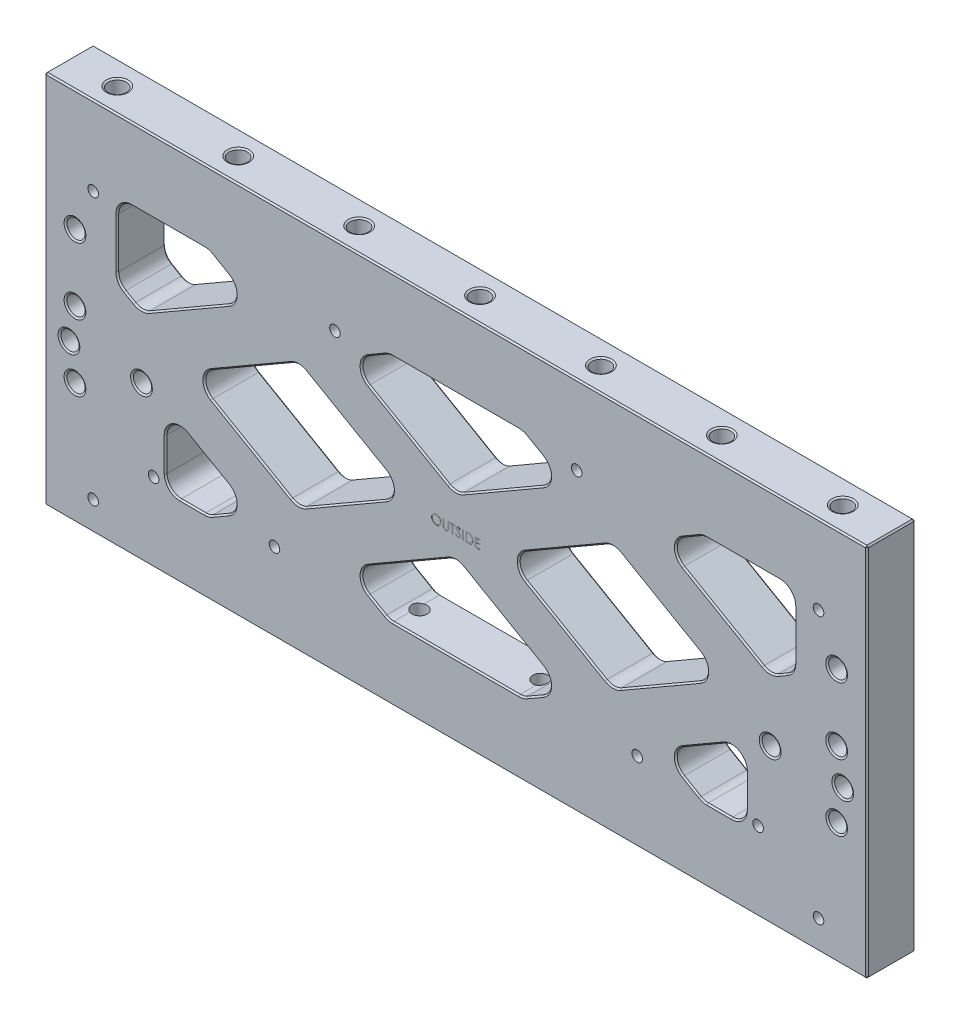
SolidWorks part; units mm, degrees
material "6061-T6 Al"
ref_plane "Front" through (0, 0, 0) normal (0, 0, 1) x (1, 0, 0)
ref_plane "Top" through (0, 0, 0) normal (0, 1, 0) x (1, 0, 0)
ref_plane "Right" through (0, 0, 0) normal (1, 0, 0) x (0, 0, -1)
sketch "Sketch1" plane through (0, 0, 0) normal (0, 0, 1) x (1, 0, 0)
  line L1 (-215.9, 196.85) -> (215.9, 196.85)
  line L2 (-215.9, 196.85) -> (-215.9, 0)
  line L3 (-215.9, 0) -> (215.9, 0)
  line L4 (215.9, 196.85) -> (215.9, 0)
  dimension "D1" = 431.8
  dimension "D2" = 196.85
extrude "Extrude1" add sketch "Sketch1" along normal blind 25.4
sketch "Sketch8" plane through (0, 0, 25.4) normal (0, 0, 1) x (1, 0, 0)
  line L0 (0, 158.75) -> (0, 196.85) construction
  line L1 (-177.8, 158.75) -> (177.8, 158.75)
  line L2 (-177.8, 158.75) -> (-177.8, 38.1)
  line L3 (-177.8, 38.1) -> (177.8, 38.1)
  line L4 (177.8, 158.75) -> (177.8, 38.1)
  line L5 (215.9, 196.85) -> (-215.9, 196.85) construction
  line L6 (0, 0) -> (0, 38.1) construction
  line L7 (-215.9, 0) -> (215.9, 0) construction
  line L8 (215.9, 0) -> (215.9, 196.85) construction
  point P4 (0, 38.1)
  dimension "D1" = 38.1
  dimension "D2" = 38.1
extrude "Extrude2" cut sketch "Sketch8" against normal through all
sketch "Sketch9" plane through (0, 0, 25.4) normal (0, 0, 1) x (1, 0, 0)
  line L0 (-129.886, 158.75) -> (79.086, 38.1)
  line L1 (177.8, 158.75) -> (-177.8, 158.75) construction
  line L2 (-177.8, 38.1) -> (177.8, 38.1) construction
  line L3 (79.086, 38.1) -> (129.886, 38.1)
  line L4 (129.886, 38.1) -> (-79.086, 158.75)
  line L5 (-79.086, 158.75) -> (-129.886, 158.75)
  line L6 (-104.486, 158.75) -> (104.486, 38.1) construction
  line L7 (-177.8, 91.0927) -> (-86.014, 38.1)
  line L8 (-177.8, 158.75) -> (-177.8, 38.1) construction
  line L9 (-86.014, 38.1) -> (-35.214, 38.1)
  line L10 (-35.214, 38.1) -> (-177.8, 120.422)
  line L11 (-177.8, 120.422) -> (-177.8, 91.0927)
  line L12 (-177.8, 91.0927) -> (-165.1, 113.0897) construction
  line L13 (-79.086, 158.75) -> (-91.786, 136.753) construction
  line L14 (35.214, 158.75) -> (177.8, 76.428)
  line L15 (177.8, 38.1) -> (177.8, 158.75) construction
  line L16 (177.8, 76.428) -> (177.8, 105.7573)
  line L17 (177.8, 105.7573) -> (86.014, 158.75)
  line L18 (86.014, 158.75) -> (35.214, 158.75)
  line L19 (86.014, 158.75) -> (73.314, 136.753) construction
  line L20 (-35.214, 38.1) -> (-6.639, 87.5934) construction
  line L21 (35.214, 158.75) -> (6.639, 109.2566) construction
  point P10 (0, 98.425)
  dimension "D1" = 30
  dimension "D2" = 25.4
  dimension "D3" = 82.55
extrude "Extrude3" add sketch "Sketch9" against normal up to surface (25.4 mm away) up to face at (0, 98.425, 0)
mirror "Mirror2" about plane through (0, 0, 0) normal (1, 0, 0) of "Extrude3"
sketch "Sketch56" plane through (0, 0, 25.4) normal (0, 0, 1) x (1, 0, 0)
  line L0 (-177.8, 76.428) -> (-177.8, 38.1)
  line L1 (-177.8, 38.1) -> (-152.4, 38.1)
  line L2 (-177.8, 38.1) -> (-129.886, 38.1) construction
  line L3 (-152.4, 38.1) -> (-152.4, 76.428)
  line L4 (-165.1, 83.7603) -> (-107.95, 50.7647) construction
  line L5 (-152.4, 76.428) -> (-165.1, 83.7603)
  line L6 (-165.1, 83.7603) -> (-177.8, 76.428)
  line L7 (-177.8, 158.75) -> (-177.8, 120.422) construction
  line L8 (0, 0) -> (0, 196.85) construction
  line L9 (215.9, 196.85) -> (-215.9, 196.85) construction
  line L10 (165.1, 83.7603) -> (177.8, 76.428)
  line L11 (152.4, 76.428) -> (165.1, 83.7603)
  line L12 (152.4, 38.1) -> (152.4, 76.428)
  line L13 (177.8, 38.1) -> (152.4, 38.1)
  line L14 (177.8, 76.428) -> (177.8, 38.1)
  dimension "D1" = 25.4
extrude "Extrude16" add sketch "Sketch56" against normal up to surface (25.4 mm away) up to face at (0, 144.552, 0)
fillet "Fillet1" radius 7.62 36 edges at (107.95, 146.0853, 12.7) (129.886, 158.75, 12.7) (177.8, 158.75, 12.7) (177.8, 120.422, 12.7) (165.1, 113.0897, 12.7) (25.4, 98.425, 12.7) (82.55, 131.4206, 12.7) (139.7, 98.425, 12.7) (82.55, 65.4294, 12.7) (35.214, 38.1, 12.7) (-35.214, 38.1, 12.7) (-57.15, 50.7647, 12.7) (0, 83.7603, 12.7) (57.15, 50.7647, 12.7) (129.886, 38.1, 12.7) (107.95, 50.7647, 12.7) (-107.95, 50.7647, 12.7) (-129.886, 38.1, 12.7) (-25.4, 98.425, 12.7) (-82.55, 65.4294, 12.7) (-82.55, 131.4206, 12.7) (-165.1, 113.0897, 12.7) (-177.8, 120.422, 12.7) (-177.8, 158.75, 12.7) (-129.886, 158.75, 12.7) (-107.95, 146.0853, 12.7) (-35.214, 158.75, 12.7) (35.214, 158.75, 12.7) (57.15, 146.0853, 12.7) (0, 113.0897, 12.7) (-57.15, 146.0853, 12.7) (-139.7, 98.425, 12.7) (152.4, 38.1, 12.7) (152.4, 76.428, 12.7) (-152.4, 38.1, 12.7) (-152.4, 76.428, 12.7)
chamfer "Chamfer2" distance 0.762 angle 45 12 edges at (-215.9, 98.425, 0) (-215.9, 98.425, 25.4) (-215.9, 0, 12.7) (0, 0, 0) (0, 0, 25.4) (215.9, 0, 12.7) (215.9, 98.425, 0) (215.9, 98.425, 25.4) (215.9, 196.85, 12.7) (0, 196.85, 0) (0, 196.85, 25.4) (-215.9, 196.85, 12.7)
chamfer "Chamfer6" distance 0.762 angle 45 144 edges at (138.3539, 38.1, 25.4) (138.3539, 38.1, 0) (150.1682, 40.3318, 0) (150.1682, 40.3318, 25.4) (129.9555, 38.3596, 0) (129.9555, 38.3596, 25.4) (152.4, 54.4749, 0) (152.4, 54.4749, 25.4) (123.7489, 41.6433, 25.4) (123.7489, 41.6433, 0) (148.59, 69.8288, 0) (148.59, 69.8288, 25.4) (115.57, 50.7647, 0) (115.57, 50.7647, 25.4) (130.175, 63.5963, 0) (130.175, 63.5963, 25.4) (165.1, 114.2685, 0) (171.45, 116.7559, 25.4) (171.45, 116.7559, 0) (140.335, 127.3878, 0) (140.335, 127.3878, 25.4) (176.7791, 121.0115, 0) (115.57, 146.0853, 0) (177.8, 137.9757, 0) (123.7489, 155.2067, 25.4) (123.7489, 155.2067, 0) (175.5682, 156.5182, 0) (129.9555, 158.4904, 0) (151.0539, 158.75, 0) (165.1, 114.2685, 25.4) (176.7791, 121.0115, 25.4) (115.57, 146.0853, 25.4) (177.8, 137.9757, 25.4) (175.5682, 156.5182, 25.4) (129.9555, 158.4904, 25.4) (151.0539, 158.75, 25.4) (107.315, 79.7275, 25.4) (107.315, 79.7275, 0) (82.55, 66.6083, 0) (132.08, 98.425, 0) (57.785, 79.7275, 25.4) (57.785, 79.7275, 0) (107.315, 117.1225, 25.4) (107.315, 117.1225, 0) (33.02, 98.425, 0) (82.55, 130.2417, 0) (57.785, 117.1225, 25.4) (57.785, 117.1225, 0) (132.08, 98.425, 25.4) (82.55, 66.6083, 25.4) (82.55, 130.2417, 25.4) (33.02, 98.425, 25.4) (0, 114.2685, 0) (24.765, 127.3878, 25.4) (24.765, 127.3878, 0) (-24.765, 127.3878, 25.4) (-24.765, 127.3878, 0) (49.53, 146.0853, 0) (-49.53, 146.0853, 0) (41.3511, 155.2067, 25.4) (41.3511, 155.2067, 0) (-41.3511, 155.2067, 0) (-41.3511, 155.2067, 25.4) (35.1445, 158.4904, 0) (-35.1445, 158.4904, 0) (0, 158.75, 0) (0, 114.2685, 25.4) (49.53, 146.0853, 25.4) (-49.53, 146.0853, 25.4) (35.1445, 158.4904, 25.4) (-35.1445, 158.4904, 25.4) (0, 158.75, 25.4) (35.1445, 38.3596, 0) (0, 38.1, 0) (41.3511, 41.6433, 0) (41.3511, 41.6433, 25.4) (-35.1445, 38.3596, 0) (49.53, 50.7647, 0) (-41.3511, 41.6433, 25.4) (-41.3511, 41.6433, 0) (24.765, 69.4622, 25.4) (24.765, 69.4622, 0) (-49.53, 50.7647, 0) (0, 82.5815, 0) (-24.765, 69.4622, 25.4) (-24.765, 69.4622, 0) (35.1445, 38.3596, 25.4) (0, 38.1, 25.4) (49.53, 50.7647, 25.4) (-35.1445, 38.3596, 25.4) (0, 82.5815, 25.4) (-49.53, 50.7647, 25.4) (-123.7489, 41.6433, 25.4) (-123.7489, 41.6433, 0) (-115.57, 50.7647, 0) (-129.9555, 38.3596, 0) (-130.175, 63.5963, 25.4) (-130.175, 63.5963, 0) (-138.3539, 38.1, 0) (-148.59, 69.8288, 0) (-150.1682, 40.3318, 0) (-152.4, 54.4749, 25.4) (-152.4, 54.4749, 0) (-129.9555, 38.3596, 25.4) (-115.57, 50.7647, 25.4) (-138.3539, 38.1, 25.4) (-150.1682, 40.3318, 25.4) (-148.59, 69.8288, 25.4) (-57.785, 79.7275, 25.4) (-57.785, 79.7275, 0) (-33.02, 98.425, 0) (-33.02, 98.425, 25.4) (-82.55, 66.6083, 25.4) (-82.55, 66.6083, 0) (-57.785, 117.1225, 25.4) (-57.785, 117.1225, 0) (-107.315, 79.7275, 25.4) (-107.315, 79.7275, 0) (-82.55, 130.2417, 25.4) (-82.55, 130.2417, 0) (-132.08, 98.425, 0) (-132.08, 98.425, 25.4) (-107.315, 117.1225, 0) (-107.315, 117.1225, 25.4) (-115.57, 146.0853, 0) (-123.7489, 155.2067, 25.4) (-123.7489, 155.2067, 0) (-140.335, 127.3878, 0) (-140.335, 127.3878, 25.4) (-129.9555, 158.4904, 0) (-165.1, 114.2685, 0) (-151.0539, 158.75, 0) (-171.45, 116.7559, 25.4) (-171.45, 116.7559, 0) (-175.5682, 156.5182, 0) (-176.7791, 121.0115, 0) (-177.8, 137.9757, 0) (-115.57, 146.0853, 25.4) (-129.9555, 158.4904, 25.4) (-165.1, 114.2685, 25.4) (-151.0539, 158.75, 25.4) (-175.5682, 156.5182, 25.4) (-176.7791, 121.0115, 25.4) (-177.8, 137.9757, 25.4)
hole_wizard "3/8-16 Tapped Hole1" positions "Sketch7" profile "Sketch6" tap size "3/8-16" standard "Ansi Inch"
sketch "Sketch7" plane through (0, 196.85, 0) normal (0, 1, 0) x (-1, 0, 0)
  line L1 (-190.5, 12.7) -> (-127, 12.7) construction
  line L2 (-127, 12.7) -> (-63.5, 12.7) construction
  line L3 (-63.5, 12.7) -> (0, 12.7) construction
  line L4 (0, 12.7) -> (63.5, 12.7) construction
  line L5 (63.5, 12.7) -> (127, 12.7) construction
  line L6 (127, 12.7) -> (190.5, 12.7) construction
  line L9 (215.9, 25.4) -> (215.9, 0) construction
  point P7 (127, 12.7)
  point P13 (0, 12.7)
  point P26 (-127, 12.7)
  point P64 (215.9, 12.7)
  dimension "D1" = 63.5
sketch "Sketch6" plane through (-127, 196.85, 12.7) normal (1, 0, 0) x (0, 0, 1)
  line L0 (0, 0) -> (0, 45.5647)
  line L1 (0, 45.5647) -> (3.9687, 43.18)
  line L2 (3.9687, 43.18) -> (3.9687, 25.4)
  line L3 (3.9687, 25.4) -> (4.7625, 25.4)
  line L5 (4.7625, 25.4) -> (4.7625, 0.5499)
  line L6 (4.7625, 0.5499) -> (5.715, 0)
  line L7 (5.715, 0) -> (0, 0)
  line L8 (-4.7625, 0.5499) -> (-5.715, 0) construction
  line L10 (0, 45.5647) -> (-3.9688, 43.18) construction
  line L11 (0, -6.35) -> (0, 107.95) construction
  dimension "Tap Drill Dia." = 7.9375
  dimension "Tap Drill Depth" = 43.18
  dimension "Thread Major Dia." = 9.525
  dimension "Thread Depth" = 25.4
  dimension "Near C'Sink Dia." = 11.43
  dimension "Near C'Sink Angle" = 120
  dimension "Drill Angle" = 118
hole_wizard "3/8-16 Tapped Hole2" positions "Sketch49" profile "Sketch48" tap size "3/8-16" standard "Ansi Inch"
sketch "Sketch49" plane through (0, 196.85, 0) normal (0, 1, 0) x (-1, 0, 0)
  point P0 (-63.5, 12.7)
  point P4 (63.5, 12.7)
  point P8 (-190.5, 12.7)
  point P10 (190.5, 12.7)
sketch "Sketch48" plane through (63.5, 196.85, 12.7) normal (1, 0, 0) x (0, 0, 1)
  line L0 (0, 0) -> (0, 45.5647)
  line L1 (0, 45.5647) -> (3.9687, 43.18)
  line L2 (3.9687, 43.18) -> (3.9687, 25.4)
  line L3 (3.9687, 25.4) -> (4.7625, 25.4)
  line L5 (4.7625, 25.4) -> (4.7625, 0.5499)
  line L6 (4.7625, 0.5499) -> (5.715, 0)
  line L7 (5.715, 0) -> (0, 0)
  line L8 (-4.7625, 0.5499) -> (-5.715, 0) construction
  line L10 (0, 45.5647) -> (-3.9688, 43.18) construction
  line L11 (0, -6.35) -> (0, 107.95) construction
  dimension "Tap Drill Dia." = 7.9375
  dimension "Tap Drill Depth" = 43.18
  dimension "Thread Major Dia." = 9.525
  dimension "Thread Depth" = 25.4
  dimension "Near C'Sink Dia." = 11.43
  dimension "Near C'Sink Angle" = 120
  dimension "Drill Angle" = 118
hole_wizard "3/8-16 Tapped Hole3" positions "Sketch27" profile "Sketch26" tap size "3/8-16" standard "Ansi Inch"
sketch "Sketch27" plane through (0, 0, 0) normal (0, -1, 0) x (1, 0, 0)
  line L0 (0, 12.7) -> (-63.5, 12.7) construction
  line L3 (63.5, 12.7) -> (0, 12.7) construction
  point P7 (-31.75, 12.7)
  point P13 (31.75, 12.7)
sketch "Sketch26" plane through (-31.75, 0, 12.7) normal (1, 0, 0) x (0, 0, -1)
  line L0 (0, 0) -> (0, 45.5647)
  line L1 (0, 45.5647) -> (3.9687, 43.18)
  line L2 (3.9687, 43.18) -> (3.9687, 25.4)
  line L3 (3.9687, 25.4) -> (4.7625, 25.4)
  line L5 (4.7625, 25.4) -> (4.7625, 0.5499)
  line L6 (4.7625, 0.5499) -> (5.715, 0)
  line L7 (5.715, 0) -> (0, 0)
  line L8 (-4.7625, 0.5499) -> (-5.715, 0) construction
  line L10 (0, 45.5647) -> (-3.9688, 43.18) construction
  line L11 (0, -6.35) -> (0, 107.95) construction
  dimension "Tap Drill Dia." = 7.9375
  dimension "Tap Drill Depth" = 43.18
  dimension "Thread Major Dia." = 9.525
  dimension "Thread Depth" = 25.4
  dimension "Near C'Sink Dia." = 11.43
  dimension "Near C'Sink Angle" = 120
  dimension "Drill Angle" = 118
hole_wizard "3/8-16 Tapped Hole4" positions "Sketch33" profile "Sketch32" tap size "3/8-16" standard "Ansi Inch"
sketch "Sketch33" plane through (0, 0, 0) normal (0, -1, 0) x (1, 0, 0)
  line L0 (-63.5, 12.7) -> (-127, 12.7) construction
  line L1 (-127, 12.7) -> (-190.5, 12.7) construction
  line L2 (127, 12.7) -> (63.5, 12.7) construction
  line L3 (190.5, 12.7) -> (127, 12.7) construction
  point P8 (-158.75, 12.7)
  point P10 (-95.25, 12.7)
  point P12 (95.25, 12.7)
  point P14 (158.75, 12.7)
sketch "Sketch32" plane through (-158.75, 0, 12.7) normal (1, 0, 0) x (0, 0, -1)
  line L0 (0, 0) -> (0, 45.5647)
  line L1 (0, 45.5647) -> (3.9687, 43.18)
  line L2 (3.9687, 43.18) -> (3.9687, 25.4)
  line L3 (3.9687, 25.4) -> (4.7625, 25.4)
  line L5 (4.7625, 25.4) -> (4.7625, 0.5499)
  line L6 (4.7625, 0.5499) -> (5.715, 0)
  line L7 (5.715, 0) -> (0, 0)
  line L8 (-4.7625, 0.5499) -> (-5.715, 0) construction
  line L10 (0, 45.5647) -> (-3.9688, 43.18) construction
  line L11 (0, -6.35) -> (0, 107.95) construction
  dimension "Tap Drill Dia." = 7.9375
  dimension "Tap Drill Depth" = 43.18
  dimension "Thread Major Dia." = 9.525
  dimension "Thread Depth" = 25.4
  dimension "Near C'Sink Dia." = 11.43
  dimension "Near C'Sink Angle" = 120
  dimension "Drill Angle" = 118
hole_wizard "7/32 (0.21875) Diameter Hole1" positions "Sketch3" profile "Sketch2" hole size "7/32" standard "Ansi Inch" end condition through all
sketch "Sketch3" plane through (0, 0, 25.4) normal (0, 0, 1) x (1, 0, 0)
  line L65 (-215.138, 196.85) -> (215.138, 196.85) construction
  line L66 (215.138, 0) -> (-215.138, 0) construction
  point P216 (-190.5, 155.448)
  point P218 (-63.5, 155.448)
  point P220 (63.5, 155.448)
  point P222 (190.5, 155.448)
  point P244 (-158.75, 41.402)
  point P246 (-95.25, 41.402)
  point P248 (95.25, 41.402)
  point P250 (158.75, 41.402)
  dimension "D1" = 41.402
  dimension "D2" = 41.402
sketch "Sketch2" plane through (-190.5, 155.448, 25.4) normal (1, 0, 0) x (0, -1, 0)
  line L0 (0, 0) -> (0, 25.4)
  line L1 (0, 25.4) -> (2.7781, 25.4)
  line L2 (2.7781, 25.4) -> (2.7781, 0)
  line L5 (2.7781, 0) -> (0, 0)
  line L11 (0, -6.35) -> (0, 107.95) construction
  dimension "Thru Hole Dia." = 5.5562
  dimension "Thru Hole Depth" = 25.4
hole_wizard "3/8-16 Tapped Hole5" positions "Sketch29" profile "Sketch28" tap size "3/8-16" standard "Ansi Inch" end condition through all
sketch "Sketch29" plane through (166.3673, -76.5124, 0) normal (0, 0, 1) x (1, 0, 0)
  line L0 (33.6577, 209.8624) -> (33.6577, 174.9374) construction
  line L1 (33.6577, 174.9374) -> (33.6577, 140.0124) construction
  line L5 (33.6577, 174.9374) -> (49.5327, 174.9374) construction
  line L7 (-382.2673, 273.3624) -> (-382.2673, 76.5124) construction
  line L8 (-366.3923, 209.8624) -> (-382.2673, 209.8624) construction
  line L9 (49.5327, 77.2744) -> (49.5327, 272.6004) construction
  line L11 (49.5327, 272.6004) -> (49.5327, 77.2744) construction
  point P0 (33.6577, 209.8624)
  point P1 (33.6577, 174.9374)
  point P3 (33.6577, 140.0124)
  point P22 (-366.3923, 209.8624)
  point P24 (-366.3923, 174.9374)
  point P26 (-366.3923, 140.0124)
  dimension "D1" = 34.925
  dimension "D2" = 15.875
sketch "Sketch28" plane through (200.025, 133.35, 0) normal (1, 0, 0) x (0, 1, 0)
  line L0 (0, 0) -> (0, 25.4)
  line L1 (0, 25.4) -> (5.715, 25.4)
  line L2 (4.7625, 24.8501) -> (4.7625, 0.5499)
  line L3 (4.7625, 0.5499) -> (5.715, 0)
  line L5 (5.715, 0) -> (0, 0)
  line L6 (-4.7625, 0.5499) -> (-5.715, 0) construction
  line L7 (5.715, 25.4) -> (4.7625, 24.8501)
  line L8 (-5.715, 25.4) -> (-4.7625, 24.8501) construction
  line L11 (0, -6.35) -> (0, 107.95) construction
  dimension "Thread Major Dia." = 9.525
  dimension "Thru Tap Drill Depth" = 25.4
  dimension "Near C'Sink Dia." = 11.43
  dimension "Near C'Sink Angle" = 120
  dimension "Far C'Sink Dia." = 11.43
  dimension "Far C'Sink Angle" = 120
hole_wizard "3/8-16 Tapped Hole6" positions "Sketch45" profile "Sketch44" tap size "3/8-16" standard "Ansi Inch" end condition through all
sketch "Sketch45" plane through (0, 0, 25.4) normal (0, 0, 1) x (1, 0, 0)
  line L0 (-203.2, 80.9625) -> (-165.1, 80.9625) construction
  line L1 (-165.1, 80.9625) -> (165.1, 80.9625) construction
  line L2 (165.1, 80.9625) -> (203.2, 80.9625) construction
  line L5 (215.138, 0) -> (-215.138, 0) construction
  line L6 (215.9, 196.088) -> (215.9, 0.762) construction
  point P0 (-203.2, 80.9625)
  point P1 (-165.1, 80.9625)
  point P3 (165.1, 80.9625)
  point P5 (203.2, 80.9625)
  point P17 (0, 80.9625)
  dimension "D1" = 38.1
  dimension "D2" = 80.9625
  dimension "D3" = 12.7
sketch "Sketch44" plane through (-203.2, 80.9625, 25.4) normal (1, 0, 0) x (0, -1, 0)
  line L0 (0, 0) -> (0, 25.4)
  line L1 (0, 25.4) -> (5.715, 25.4)
  line L2 (4.7625, 24.8501) -> (4.7625, 0.5499)
  line L3 (4.7625, 0.5499) -> (5.715, 0)
  line L5 (5.715, 0) -> (0, 0)
  line L6 (-4.7625, 0.5499) -> (-5.715, 0) construction
  line L7 (5.715, 25.4) -> (4.7625, 24.8501)
  line L8 (-5.715, 25.4) -> (-4.7625, 24.8501) construction
  line L11 (0, -6.35) -> (0, 107.95) construction
  dimension "Thread Major Dia." = 9.525
  dimension "Thru Tap Drill Depth" = 25.4
  dimension "Near C'Sink Dia." = 11.43
  dimension "Near C'Sink Angle" = 120
  dimension "Far C'Sink Dia." = 11.43
  dimension "Far C'Sink Angle" = 120
hole_wizard "3/8 (0.375) Diameter Hole1" positions "Sketch52" profile "Sketch51" hole size "3/8" standard "Ansi Inch"
sketch "Sketch52" plane through (0, 0, 0) normal (0, -1, 0) x (1, 0, 0)
  line L1 (0, 0) -> (0, 25.4) construction
  line L2 (-215.138, 25.4) -> (215.138, 25.4) construction
  point P0 (-190.5, 12.7)
  point P16 (0, 12.7)
  dimension "D1" = 381
sketch "Sketch51" plane through (-190.5, 0, 12.7) normal (1, 0, 0) x (0, 0, -1)
  line L0 (0, 0) -> (0, 21.9169)
  line L1 (0, 21.9169) -> (4.7714, 19.05)
  line L2 (4.7714, 19.05) -> (4.7714, 2.3406)
  line L3 (4.7714, 2.3406) -> (7.112, 0)
  line L5 (7.112, 0) -> (0, 0)
  line L6 (-4.7714, 2.3406) -> (-7.112, 0) construction
  line L10 (0, 21.9169) -> (-4.7714, 19.05) construction
  line L11 (0, -6.35) -> (0, 107.95) construction
  dimension "Hole Dia." = 9.5428
  dimension "Hole Depth" = 19.05
  dimension "Near C'Sink Dia." = 14.224
  dimension "Near C'Sink Angle" = 90
  dimension "Drill Angle" = 118
sketch "Sketch53" plane through (0, 0, 0) normal (0, -1, 0) x (1, 0, 0)
  line L0 (187.96, 12.7) -> (193.04, 12.7) construction
  line L1 (187.96, 17.4714) -> (193.04, 17.4714)
  line L2 (187.96, 7.9286) -> (193.04, 7.9286)
  line L3 (-190.5, 12.7) -> (190.5, 12.7) construction
  line L4 (0, -13.97) -> (0, 13.97) construction
  arc A0 (187.96, 17.4714) -> (187.96, 7.9286) centre (187.96, 12.7) ccw
  arc A1 (193.04, 7.9286) -> (193.04, 17.4714) centre (193.04, 12.7) ccw
  circle A2 centre (-190.5, 12.7) radius 4.7714 construction
  point P2 (190.5, 12.7)
  point P14 (0, 12.7)
  dimension "D2" = 5.08
extrude "Extrude15" cut sketch "Sketch53" against normal blind 19.05
chamfer "Chamfer5" distance 2.286 angle 45 4 edges at (197.8114, 0, 12.7) (190.5, 0, 17.4714) (190.5, 0, 7.9286) (183.1886, 0, 12.7)
hole_wizard "7/32 (0.21875) Diameter Hole2" positions "Sketch55" profile "Sketch54" hole size "7/32" standard "Ansi Inch" end condition through all
sketch "Sketch55" plane through (0, 0, 25.4) normal (0, 0, 1) x (1, 0, 0)
  line L0 (215.138, 0) -> (-215.138, 0) construction
  point P0 (-190.5, 15.24)
  point P1 (190.5, 15.24)
  dimension "D1" = 15.24
sketch "Sketch54" plane through (-190.5, 15.24, 25.4) normal (1, 0, 0) x (0, -1, 0)
  line L0 (0, 0) -> (0, 25.4)
  line L1 (0, 25.4) -> (2.7781, 25.4)
  line L2 (2.7781, 25.4) -> (2.7781, 0)
  line L5 (2.7781, 0) -> (0, 0)
  line L11 (0, -6.35) -> (0, 107.95) construction
  dimension "Thru Hole Dia." = 5.5562
  dimension "Thru Hole Depth" = 25.4
sketch "Sketch59" plane through (0, 0, 25.4) normal (0, 0, 1) x (1, 0, 0)
  line L0 (-17.9428, 93.8503) -> (17.9428, 93.8503) construction
  line L1 (0, 83.3435) -> (0, 93.8503) construction
  arc A0 (4.191, 82.2205) -> (-4.191, 82.2205) centre (0, 74.9615) ccw construction
  text T0 "OUTSIDE" font "Century Gothic" height in points 18
extrude "Extrude17" cut sketch "Sketch59" against normal blind 0.0254
